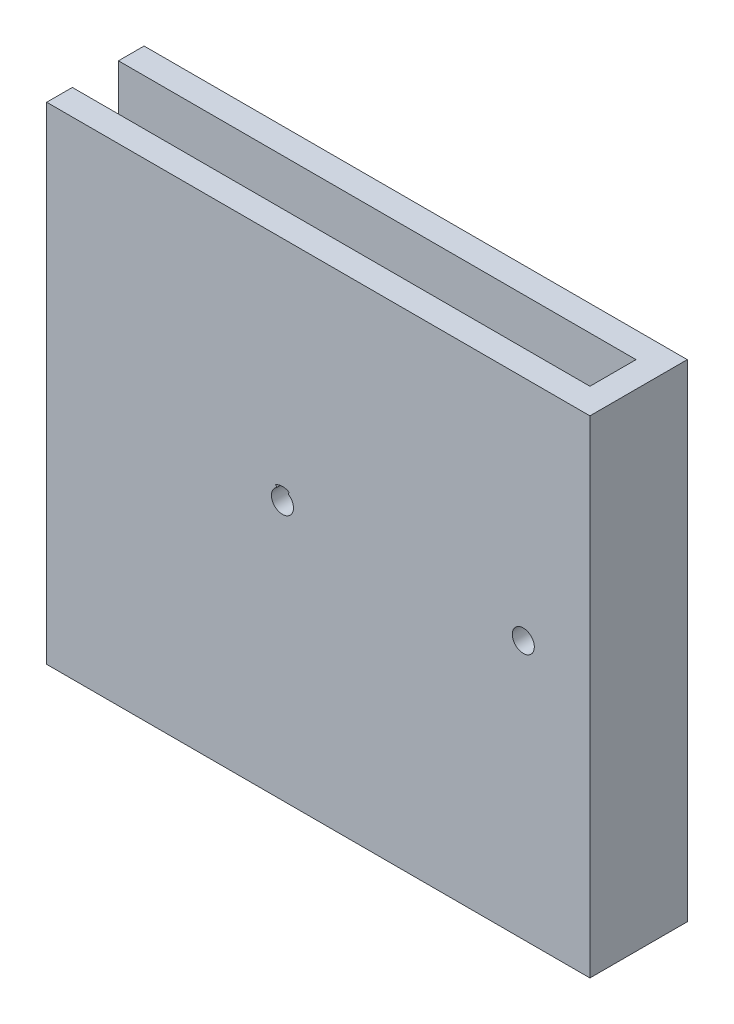
SolidWorks part; units mm, degrees
ref_plane "Front Plane" through (0, 0, 0) normal (0, 0, 1) x (1, 0, 0)
ref_plane "Top Plane" through (0, 0, 0) normal (0, 1, 0) x (1, 0, 0)
ref_plane "Right Plane" through (0, 0, 0) normal (1, 0, 0) x (0, 0, -1)
sketch "Sketch1" plane through (0, 0, 0) normal (0, 0, 1) x (1, 0, 0)
  line L1 (-20.1463, 55.4268) -> (80.8537, 55.4268)
  line L2 (-20.1463, 55.4268) -> (-20.1463, -34.5732)
  line L3 (-20.1463, -34.5732) -> (80.8537, -34.5732)
  line L4 (80.8537, 55.4268) -> (80.8537, -34.5732)
  dimension "D1" = 90
  dimension "D2" = 101
extrude "Boss-Extrude1" add sketch "Sketch1" along normal blind 5 contours L1 L4 L3 L2
sketch "Sketch2" plane through (80.8537, 0, 0) normal (1, 0, 0) x (0, 0, -1)
  line L1 (-5, 55.4268) -> (9, 55.4268)
  line L2 (-5, 55.4268) -> (-5, -34.5732)
  line L3 (-5, -34.5732) -> (9, -34.5732)
  line L4 (9, 55.4268) -> (9, -34.5732)
  dimension "D1" = 14
extrude "Boss-Extrude2" add sketch "Sketch2" along normal blind 5
sketch "Sketch3" plane through (0, 0, -9) normal (0, 0, -1) x (-1, 0, 0)
  line L1 (-85.8537, 55.4268) -> (20.1463, 55.4268)
  line L2 (-85.8537, 55.4268) -> (-85.8537, -34.5732)
  line L3 (-85.8537, -34.5732) -> (20.1463, -34.5732)
  line L4 (20.1463, 55.4268) -> (20.1463, -34.5732)
extrude "Boss-Extrude3" add sketch "Sketch3" along normal blind 5
sketch "Sketch4" plane through (0, -34.5732, 0) normal (0, -1, 0) x (1, 0, 0)
  line L0 (-20.1463, 0) -> (80.8537, 0) construction
  line L1 (-20.1463, 5) -> (85.8537, 5)
  line L2 (-20.1463, 5) -> (-20.1463, -14)
  line L3 (-20.1463, -14) -> (85.8537, -14)
  line L4 (85.8537, 5) -> (85.8537, -14)
  line L5 (80.8537, 0) -> (80.8537, -9) construction
  line L6 (80.8537, -9) -> (-20.1463, -9) construction
extrude "Boss-Extrude4" add sketch "Sketch4" along normal blind 5
sketch "Sketch5" plane through (0, 0, -14) normal (0, 0, -1) x (-1, 0, 0)
  line L0 (-85.8537, 55.4268) -> (-85.8537, -39.5732) construction
  line L2 (20.1463, 55.4268) -> (-85.8537, 55.4268) construction
  circle A0 centre (-72.8537, 10.9268) radius 2.15
  circle A1 centre (-25.8537, 10.9268) radius 2.15
  dimension "D1" = 4.3
  dimension "D2" = 4.3
  dimension "D3" = 13
  dimension "D4" = 47
  dimension "D5" = 44.5
  dimension "D6" = 44.5
extrude "Cut-Extrude1" cut sketch "Sketch5" against normal through all
sketch "Sketch6" plane through (0, 0, -14) normal (0, 0, -1) x (-1, 0, 0)
  line L1 (-72.8537, 10.9268) -> (-71.5249, 13.1383)
  line L2 (-72.8537, 10.9268) -> (-74.1825, 13.1383)
  arc A0 (-71.5249, 13.1383) -> (-74.1825, 13.1383) centre (-72.8537, 10.9268) ccw
  circle A1 centre (-72.8537, 10.9268) radius 2.15 construction
  dimension "D1" = 0.43
extrude "Cut-Extrude2" cut sketch "Sketch6" against normal blind 10
sketch "Sketch7" plane through (0, 0, 5) normal (0, 0, 1) x (1, 0, 0)
  line L1 (25.8537, 10.9268) -> (27.1825, 13.1383)
  line L2 (25.8537, 10.9268) -> (24.5249, 13.1383)
  arc A0 (27.1825, 13.1383) -> (24.5249, 13.1383) centre (25.8537, 10.9268) ccw
  circle A1 centre (25.8537, 10.9268) radius 2.15 construction
  dimension "D1" = 0.43
extrude "Cut-Extrude3" cut sketch "Sketch7" against normal blind 10
